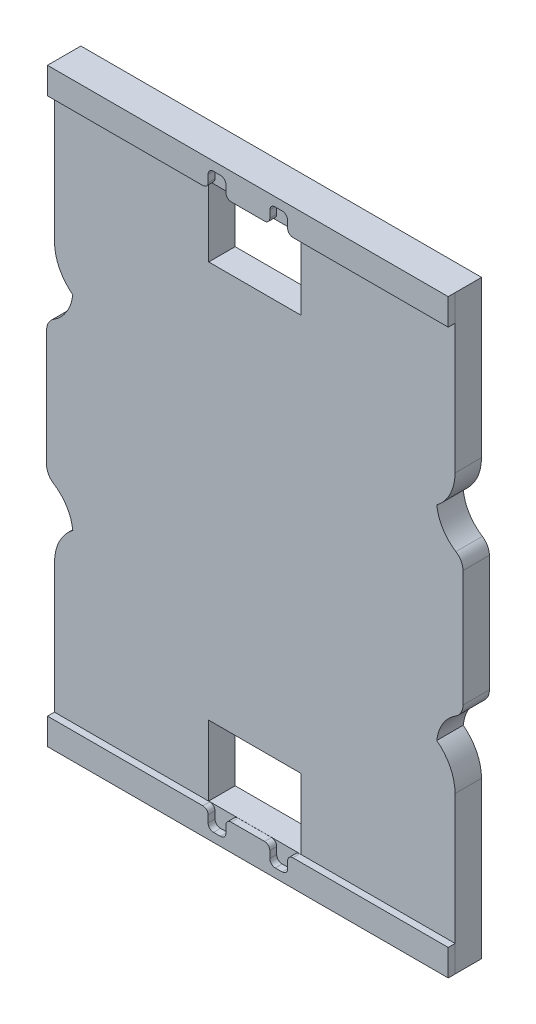
SolidWorks part; units mm, degrees
ref_plane "Front Plane" through (0, 0, 0) normal (0, 0, 1) x (1, 0, 0)
ref_plane "Top Plane" through (0, 0, 0) normal (0, 1, 0) x (1, 0, 0)
ref_plane "Right Plane" through (0, 0, 0) normal (1, 0, 0) x (0, 0, -1)
sketch "Sketch1" plane through (0, 0, 7.67) normal (0, 0, 1) x (1, 0, 0)
  line L12 (-10.2, 60.925) -> (-45.45, 60.925)
  line L13 (-45.45, 31.4857) -> (-45.45, 150) construction
  line L14 (-3.8, 60.925) -> (3.8, 60.925)
  line L15 (-4.975, 63.7) -> (-4.975, 62.1)
  line L16 (-7.8, 64.925) -> (-6.2, 64.925)
  line L17 (-9.025, 62.1) -> (-9.025, 63.7)
  line L18 (-4.975, 63.7) -> (-4.975, 62.1)
  line L19 (-7.8, 64.925) -> (-6.2, 64.925)
  line L20 (-9.025, 62.1) -> (-9.025, 63.7)
  line L21 (-60, 60.9) -> (60, 60.9) construction
  line L22 (0, 60.95) -> (0, 30.45) construction
  line L23 (-45.45, 60.925) -> (-45.45, 66.925)
  line L24 (-45.45, 66.925) -> (45.45, 66.925)
  line L25 (-47.25, 0) -> (0, 0) construction
  line L26 (45.45, 60.925) -> (45.45, 66.925)
  line L27 (9.025, 62.1) -> (9.025, 63.7)
  line L28 (7.8, 64.925) -> (6.2, 64.925)
  line L29 (4.975, 63.7) -> (4.975, 62.1)
  line L30 (10.2, 60.925) -> (45.45, 60.925)
  line L31 (10.2, -60.925) -> (45.45, -60.925)
  line L32 (4.975, -63.7) -> (4.975, -62.1)
  line L33 (7.8, -64.925) -> (6.2, -64.925)
  line L34 (9.025, -62.1) -> (9.025, -63.7)
  line L35 (45.45, -60.925) -> (45.45, -66.925)
  line L36 (-45.45, -66.925) -> (45.45, -66.925)
  line L37 (-45.45, -60.925) -> (-45.45, -66.925)
  line L38 (-9.025, -62.1) -> (-9.025, -63.7)
  line L39 (-7.8, -64.925) -> (-6.2, -64.925)
  line L40 (-4.975, -63.7) -> (-4.975, -62.1)
  line L41 (-3.8, -60.925) -> (3.8, -60.925)
  line L42 (-10.2, -60.925) -> (-45.45, -60.925)
  arc A16 (10.2, 60.925) -> (9.025, 62.1) centre (10.2, 62.1) cw
  arc A17 (7.8, 64.925) -> (9.025, 63.7) centre (7.8, 63.7) cw
  arc A18 (4.975, 63.7) -> (6.2, 64.925) centre (6.2, 63.7) cw
  arc A19 (4.975, 62.1) -> (3.8, 60.925) centre (3.8, 62.1) cw
  arc A20 (-4.975, 62.1) -> (-3.8, 60.925) centre (-3.8, 62.1) ccw
  arc A21 (-4.975, 63.7) -> (-6.2, 64.925) centre (-6.2, 63.7) ccw
  arc A22 (-7.8, 64.925) -> (-9.025, 63.7) centre (-7.8, 63.7) ccw
  arc A23 (-10.2, 60.925) -> (-9.025, 62.1) centre (-10.2, 62.1) ccw
  arc A24 (-4.975, 62.1) -> (-3.8, 60.925) centre (-3.8, 62.1) ccw
  arc A25 (-4.975, 63.7) -> (-6.2, 64.925) centre (-6.2, 63.7) ccw
  arc A26 (-7.8, 64.925) -> (-9.025, 63.7) centre (-7.8, 63.7) ccw
  arc A27 (-10.2, 60.925) -> (-9.025, 62.1) centre (-10.2, 62.1) ccw
  arc A28 (-10.2, -60.925) -> (-9.025, -62.1) centre (-10.2, -62.1) cw
  arc A29 (-7.8, -64.925) -> (-9.025, -63.7) centre (-7.8, -63.7) cw
  arc A30 (-4.975, -63.7) -> (-6.2, -64.925) centre (-6.2, -63.7) cw
  arc A31 (-4.975, -62.1) -> (-3.8, -60.925) centre (-3.8, -62.1) cw
  arc A32 (4.975, -62.1) -> (3.8, -60.925) centre (3.8, -62.1) ccw
  arc A33 (4.975, -63.7) -> (6.2, -64.925) centre (6.2, -63.7) ccw
  arc A34 (7.8, -64.925) -> (9.025, -63.7) centre (7.8, -63.7) ccw
  arc A35 (10.2, -60.925) -> (9.025, -62.1) centre (10.2, -62.1) ccw
  point P6 (0, 60.9)
  point P28 (0, 66.925)
  point P29 (0, 60.925)
  point P59 (0, -60.925)
  point P61 (0, -66.925)
  dimension "D2" = 2
  dimension "D1" = 0.025
extrude "Boss-Extrude1" add sketch "Sketch1" against normal up to surface (1.57 mm away)
sketch "Sketch2" plane through (0, 0, 0.1) normal (0, 0, 1) x (1, 0, 0)
  line L0 (60, 0) -> (-60, 0) construction
  line L1 (-47.225, -13.2107) -> (-47.225, -0.025)
  line L2 (47.225, -0.025) -> (47.225, -13.2107)
  line L3 (-47.225, -0.025) -> (47.225, -0.025)
  line L4 (45.45, -66.925) -> (45.425, -31.4857)
  line L5 (-45.45, -66.925) -> (45.45, -66.925)
  line L6 (-45.425, 31.4857) -> (-45.45, 66.925)
  line L7 (-45.45, 66.925) -> (45.45, 66.925)
  line L8 (45.45, 66.925) -> (45.425, 31.4857)
  line L9 (-45.425, -31.4857) -> (-45.45, -66.925)
  line L10 (-47.225, -0.025) -> (-47.225, 0.025)
  line L11 (47.225, -0.025) -> (47.225, 0.025)
  line L12 (-47.225, 0.025) -> (47.225, 0.025)
  line L13 (47.225, 0.025) -> (47.225, 13.2107)
  line L14 (45.425, 31.4857) -> (45.425, 150)
  line L15 (34.95, 160.475) -> (-34.95, 160.475)
  line L16 (-45.425, 150) -> (-45.425, 31.4857)
  line L17 (-47.225, 13.2107) -> (-47.225, 0.025)
  line L18 (-47.225, 0.025) -> (47.225, 0.025)
  line L19 (47.225, 0.025) -> (47.225, 13.2107)
  line L23 (-47.225, 13.2107) -> (-47.225, 0.025)
  line L24 (-10.45, -45) -> (10.45, -45)
  line L25 (10.45, -45) -> (10.45, -60.9)
  line L26 (10.45, -103) -> (10.45, -45) construction
  line L27 (10.45, -60.9) -> (-10.45, -60.9)
  line L28 (-10.45, -45) -> (-10.45, -103) construction
  line L29 (-10.45, -60.9) -> (-10.45, -45)
  line L31 (60, -60.9) -> (-60, -60.9) construction
  line L32 (-10.45, 60.9) -> (-10.45, 45)
  line L33 (10.45, 60.9) -> (-10.45, 60.9)
  line L34 (10.45, 45) -> (10.45, 60.9)
  line L35 (-10.45, 45) -> (10.45, 45)
  arc A0 (-45.6212, -16.1389) -> (-47.225, -13.2107) centre (-43.75, -13.2107) cw
  arc A1 (-45.6212, -16.1389) -> (-41.2803, -23.1399) centre (-50.75, -24.1652) cw
  arc A2 (-45.425, -31.4857) -> (-41.2803, -23.1399) centre (-34.95, -31.4857) cw
  arc A3 (41.2803, -23.1399) -> (45.425, -31.4857) centre (34.95, -31.4857) cw
  arc A4 (41.2803, -23.1399) -> (45.6212, -16.1389) centre (50.75, -24.1652) cw
  arc A5 (47.225, -13.2107) -> (45.6212, -16.1389) centre (43.75, -13.2107) cw
  arc A16 (47.225, 13.2107) -> (45.6212, 16.1389) centre (43.75, 13.2107) ccw
  arc A17 (41.2803, 23.1399) -> (45.6212, 16.1389) centre (50.75, 24.1652) ccw
  arc A18 (41.2803, 23.1399) -> (45.425, 31.4857) centre (34.95, 31.4857) ccw
  arc A19 (45.425, 150) -> (34.95, 160.475) centre (34.95, 150) ccw
  arc A20 (-34.95, 160.475) -> (-45.425, 150) centre (-34.95, 150) ccw
  arc A21 (-45.425, 31.4857) -> (-41.2803, 23.1399) centre (-34.95, 31.4857) ccw
  arc A22 (-45.6212, 16.1389) -> (-41.2803, 23.1399) centre (-50.75, 24.1652) ccw
  arc A23 (-45.6212, 16.1389) -> (-47.225, 13.2107) centre (-43.75, 13.2107) ccw
  arc A24 (47.225, 13.2107) -> (45.6212, 16.1389) centre (43.75, 13.2107) ccw
  arc A25 (41.2803, 23.1399) -> (45.6212, 16.1389) centre (50.75, 24.1652) ccw
  arc A26 (41.2803, 23.1399) -> (45.425, 31.4857) centre (34.95, 31.4857) ccw
  arc A29 (-45.425, 31.4857) -> (-41.2803, 23.1399) centre (-34.95, 31.4857) ccw
  arc A30 (-45.6212, 16.1389) -> (-41.2803, 23.1399) centre (-50.75, 24.1652) ccw
  arc A31 (-45.6212, 16.1389) -> (-47.225, 13.2107) centre (-43.75, 13.2107) ccw
  line M15 (10.45, -103) -> (10.45, -45)
  line M16 (10.45, -45) -> (30.45, -45)
  line M17 (30.45, -45) -> (30.45, -103)
  line M20 (-30.45, -103) -> (-30.45, -45)
  line M21 (-30.45, -45) -> (-10.45, -45)
  line M22 (-10.45, -45) -> (-10.45, -103)
  line M24 (47.25, 0) -> (-47.25, 0)
  dimension "D1" = 0.025
extrude "Boss-Extrude3" add sketch "Sketch2" along normal up to surface (6 mm away) contours A30 A31 L23 L18 L19 A24 A25 A26 L8 L7 L6 A29 L35 L32 L33 L34 | L18 L10 L11 M24 | L3 L11 L10 M24 | A5 L2 L3 L1 A0 A1 A2 L9 L5 L24 L4 A3 A4 M20 M21 M16 M17 | L5 M15 M17 M16 | L5 M20 M22 M21 | L27 L5 M15 M22 up to face at (0, 63.1171, 6.1)
